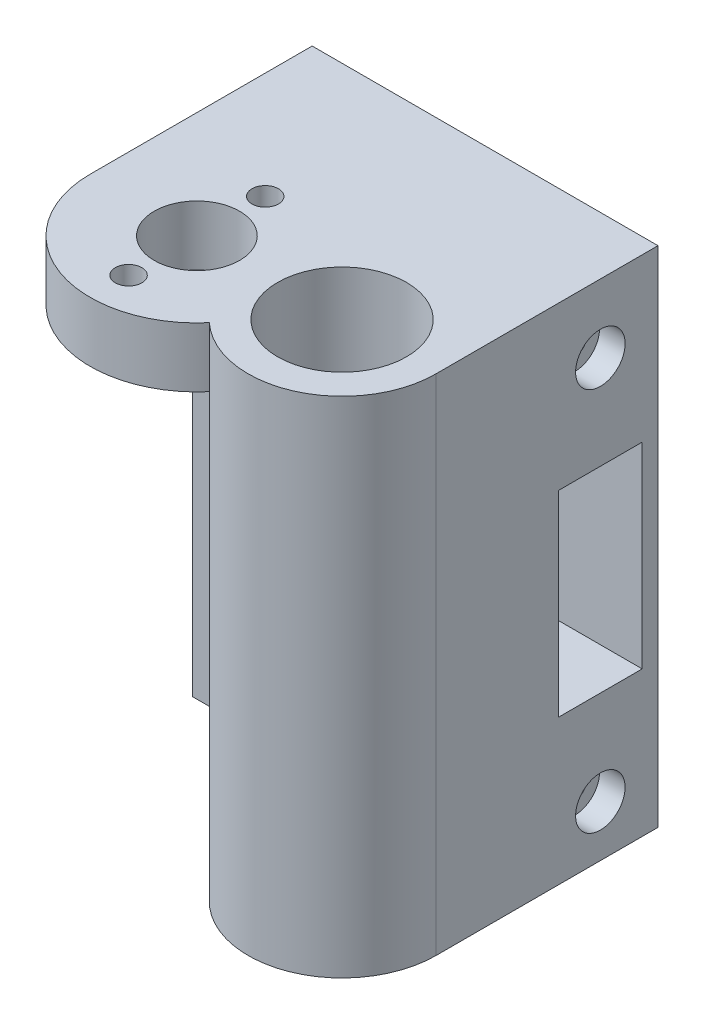
SolidWorks part; units mm, degrees
ref_plane "Alzado" through (0, 0, 0) normal (0, 0, 1) x (1, 0, 0)
ref_plane "Planta" through (0, 0, 0) normal (0, 1, 0) x (1, 0, 0)
ref_plane "Vista lateral" through (0, 0, 0) normal (1, 0, 0) x (0, 0, -1)
sketch "Croquis1" plane through (0, 0, 0) normal (0, 1, 0) x (1, 0, 0)
  line L0 (28, 0) -> (28, 26)
  line L1 (-12.5, 0) -> (-12.5, 26)
  line L2 (-12.5, 26) -> (28, 26)
  circle A0 centre (0, 0) radius 5
  circle A1 centre (17, 0) radius 7.55
  arc A2 (-12.5, 0) -> (9.5368, -8.0808) centre (0, 0) ccw
  arc A3 (9.5368, -8.0808) -> (28, 0) centre (17, 0) ccw
  dimension "D1" = 10
  dimension "D2" = 15.1
  dimension "D4" = 25
  dimension "D5" = 22
  dimension "D3" = 17
  dimension "D6" = 26
extrude "Saliente-Extruir1" add sketch "Croquis1" along normal blind 7
sketch "Croquis4" plane through (0, 0, 0) normal (0, -1, 0) x (1, 0, 0)
  line L1 (28, 0) -> (28, -26) construction
  line L2 (-12.5, -26) -> (28, -26)
  line L3 (28, 0) -> (28, -26)
  line L4 (6, 0) -> (6, -12)
  line L5 (-12.5, -12) -> (6, -12)
  line L6 (-12.5, -26) -> (-12.5, 0) construction
  arc A0 (28, 0) -> (9.5368, 8.0808) centre (17, 0) ccw construction
  arc A1 (28, 0) -> (9.5368, 8.0808) centre (17, 0) ccw
  arc A2 (28, 0) -> (6, 0) centre (17, 0) ccw
  circle A3 centre (17, 0) radius 7.55
  arc M1 (28, 0) -> (9.5368, 8.0808) centre (17, 0) ccw
  line M3 (-12.5, 0) -> (-12.5, -26)
  line M4 (-12.5, -26) -> (28, -26)
  line M5 (28, -26) -> (28, 0)
  circle M7 centre (17, 0) radius 7.55
  dimension "D1" = 15.1
  dimension "D2" = 14
extrude "Saliente-Extruir4" add sketch "Croquis4" along normal blind 52 contours A2 L4 L5 M1 M3 M4 M5 M7
sketch "Croquis5" plane through (-12.5, 0, 0) normal (-1, 0, 0) x (0, 0, 1)
  line L0 (-26, 7) -> (-26, -52) construction
  line L1 (-26, 7) -> (0, 7) construction
  circle A0 centre (-19.25, -1) radius 4.1
  circle A1 centre (-19.25, -46) radius 4.1
  dimension "D1" = 8.2
  dimension "D2" = 8.2
  dimension "D3" = 45
  dimension "D4" = 6.75
  dimension "D5" = 8
extrude "Cortar-Extruir1" cut sketch "Croquis5" against normal blind 35
sketch "Croquis6" plane through (-12.5, 0, 0) normal (-1, 0, 0) x (0, 0, 1)
  line L0 (-26, 7) -> (-26, -52) construction
  line L1 (-24.15, -35) -> (-14.35, -35)
  line L2 (-24.15, -35) -> (-24.15, -12)
  line L3 (-24.15, -12) -> (-14.35, -12)
  line L4 (-14.35, -35) -> (-14.35, -12)
  line L5 (-24.15, -35) -> (-14.35, -12) construction
  line L6 (-24.15, -12) -> (-14.35, -35) construction
  circle A0 centre (-19.25, -1) radius 4.1 construction
  circle A1 centre (-19.25, -1) radius 4.1 construction
  point P0 (-19.25, -23.5)
  dimension "D1" = 9.8
  dimension "D2" = 23
  dimension "D3" = 6.75
  dimension "D4" = 22.5
extrude "Cortar-Extruir2" cut sketch "Croquis6" against normal through all
sketch "Croquis7" plane through (28, 0, 0) normal (1, 0, 0) x (0, 0, -1)
  circle A0 centre (19.25, -1) radius 4.1 construction
  circle A1 centre (19.25, -1) radius 4.1 construction
  circle A2 centre (19.25, -46) radius 4.1 construction
  circle A3 centre (19.25, -46) radius 4.1 construction
  circle A4 centre (19.25, -1) radius 1.4
  circle A5 centre (19.25, -46) radius 1.4
  dimension "D1" = 2.8
  dimension "D2" = 2.8
extrude "Cortar-Extruir3" cut sketch "Croquis7" against normal through all
sketch "Croquis8" plane through (28, 0, 0) normal (1, 0, 0) x (0, 0, -1)
  circle A0 centre (19.25, -1) radius 1.4 construction
  circle A1 centre (19.25, -1) radius 1.4
  circle A2 centre (19.25, -46) radius 1.4 construction
  circle A3 centre (19.25, -46) radius 1.4
  circle A4 centre (19.25, -1) radius 2.9
  circle A5 centre (19.25, -46) radius 2.9
  dimension "D1" = 5.8
  dimension "D2" = 5.8
extrude "Cortar-Extruir4" cut sketch "Croquis8" against normal blind 3
sketch "Croquis10" plane through (0, 0, -12) normal (0, 0, 1) x (1, 0, 0)
  line L0 (-12.5, -52) -> (6, -52) construction
  line L1 (-12.5, -52) -> (-12.5, 0) construction
  circle A0 centre (-5.5, -23.5) radius 1.5
  point P4 (-3.25, -52)
  dimension "D1" = 3
  dimension "D2" = 28.5
  dimension "D3" = 7
extrude "Cortar-Extruir5" cut sketch "Croquis10" against normal through all
sketch "Croquis11" plane through (0, 7, 0) normal (0, 1, 0) x (1, 0, 0)
  circle A0 centre (0, 0) radius 5 construction
  circle A1 centre (0, 0) radius 5 construction
  circle A2 centre (0, 0) radius 8 construction
  circle A3 centre (0, 8) radius 1.55
  circle A4 centre (0, -8) radius 1.55
  dimension "D1" = 16
  dimension "D2" = 3.1
  dimension "D3" = 3.1
extrude "Cortar-Extruir6" cut sketch "Croquis11" against normal through all
